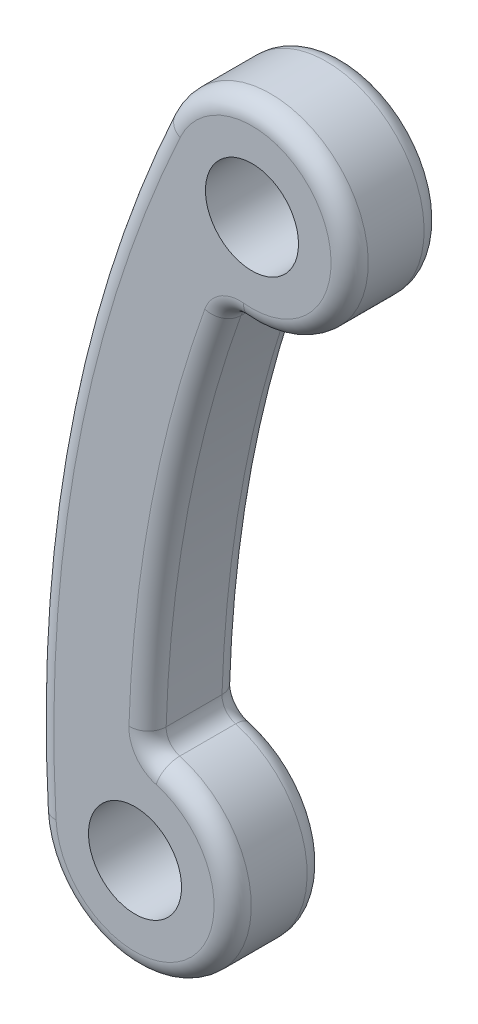
SolidWorks part; units mm, degrees
ref_plane "Front Plane" through (0, 0, 0) normal (0, 0, 1) x (1, 0, 0)
ref_plane "Top Plane" through (0, 0, 0) normal (0, 1, 0) x (1, 0, 0)
ref_plane "Right Plane" through (0, 0, 0) normal (1, 0, 0) x (0, 0, -1)
sketch "Sketch2" plane through (0, 0, 0) normal (0, 0, 1) x (1, 0, 0)
  arc A0 (-136.2482, 62.7409) -> (-149.7649, -8.3949) centre (0, 0) ccw
  arc A2 (-129.3171, 48.1776) -> (-136.2482, 62.7409) centre (-126.7108, 58.349) ccw
  arc A3 (-149.7649, -8.3949) -> (-137.9753, 2.6112) centre (-139.2814, -7.8073) ccw
  circle A4 centre (-126.7108, 58.349) radius 5
  circle A5 centre (-139.2814, -7.8073) radius 5
  arc A6 (-129.3171, 48.1776) -> (-137.9753, 2.6112) centre (0, 0) ccw
  dimension "D1" = 300
  dimension "D3" = 21
  dimension "D4" = 21
  dimension "D6" = 10
  dimension "D7" = 10
  dimension "D5" = 67.34
extrude "Boss-Extrude1" add sketch "Sketch2" along normal blind 10
fillet "Fillet1" radius 2 10 edges at (-117.2299, 62.8613, 10) (-147.3633, 28.0008, 10) (-117.2299, 62.8613, 0) (-147.3633, 28.0008, 0) (-132.1162, -15.4825, 10) (-132.1162, -15.4825, 0) (-137.9753, 2.6112, 5) (-135.5743, 25.7608, 10) (-129.3171, 48.1776, 5) (-135.5743, 25.7608, 0)
